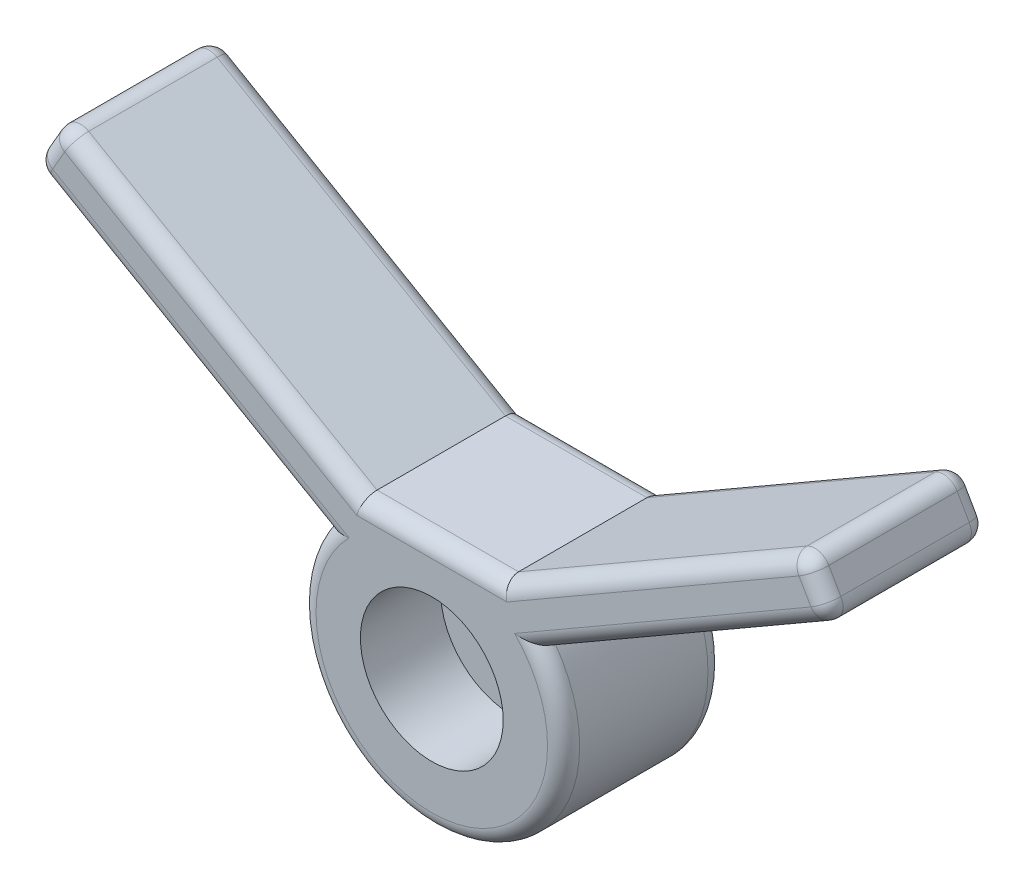
SolidWorks part; units mm, degrees
ref_plane "Front Plane" through (0, 0, 0) normal (0, 0, 1) x (1, 0, 0)
ref_plane "Top Plane" through (0, 0, 0) normal (0, 1, 0) x (1, 0, 0)
ref_plane "Right Plane" through (0, 0, 0) normal (1, 0, 0) x (0, 0, -1)
sketch "Sketch2" plane through (0, 0, 0) normal (0, 0, 1) x (1, 0, 0)
  line L1 (16.9846, 2.4737) -> (63.5, 29.3294)
  line L2 (63.5, 29.3294) -> (59.055, 37.0284)
  line L3 (59.055, 37.0284) -> (11.202, 9.4004)
  line L4 (11.202, 9.4004) -> (-11.202, 9.4004)
  line L5 (0, 9.4004) -> (0, 0) construction
  line L6 (-63.5, 29.3294) -> (-59.055, 37.0284)
  line L7 (-59.055, 37.0284) -> (-11.202, 9.4004)
  line L8 (-16.9846, 2.4737) -> (-63.5, 29.3294)
  line L12 (0, -9.6496) -> (-20.8674, -9.6496) construction
  line L13 (0, -9.6496) -> (0, -30.517) construction
  line L21 (0, -9.6496) -> (16.9846, 2.4737) construction
  circle A0 centre (0, -9.6496) radius 3.9688
  arc A1 (16.9846, 2.4737) -> (-16.9846, 2.4737) centre (0, -9.6496) cw
  dimension "D2" = 7.9375
  dimension "D4" = 8.89
  dimension "D5" = 90
  dimension "D6" = 150
  dimension "D8" = 19.05
extrude "Boss-Extrude1" add sketch "Sketch2" along normal blind 25.4
fillet "Fillet3" radius 2.54 20 edges at (0, -30.517, 25.4) (-40.2423, 15.9015, 25.4) (-63.5, 29.3294, 12.7) (-59.055, 37.0284, 12.7) (-35.1285, 23.2144, 25.4) (-35.1285, 23.2144, 0) (-40.2423, 15.9015, 0) (35.1285, 23.2144, 0) (40.2423, 15.9015, 0) (63.5, 29.3294, 12.7) (59.055, 37.0284, 12.7) (61.2775, 33.1789, 0) (61.2775, 33.1789, 25.4) (40.2423, 15.9015, 25.4) (35.1285, 23.2144, 25.4) (0, 9.4004, 0) (0, 9.4004, 25.4) (0, -30.517, 0) (-61.2775, 33.1789, 25.4) (-61.2775, 33.1789, 0)
sketch "Sketch3" plane through (0, 0, 25.4) normal (0, 0, 1) x (1, 0, 0)
  line L0 (-18.3274, -9.6496) -> (18.3274, -9.6496) construction
  arc A0 (-13.1024, 3.1653) -> (13.1024, 3.1653) centre (0, -9.6496) ccw construction
  circle A1 centre (0, -9.6496) radius 11.303
  dimension "D1" = 22.606
extrude "Cut-Extrude1" cut sketch "Sketch3" against normal blind 12.7
